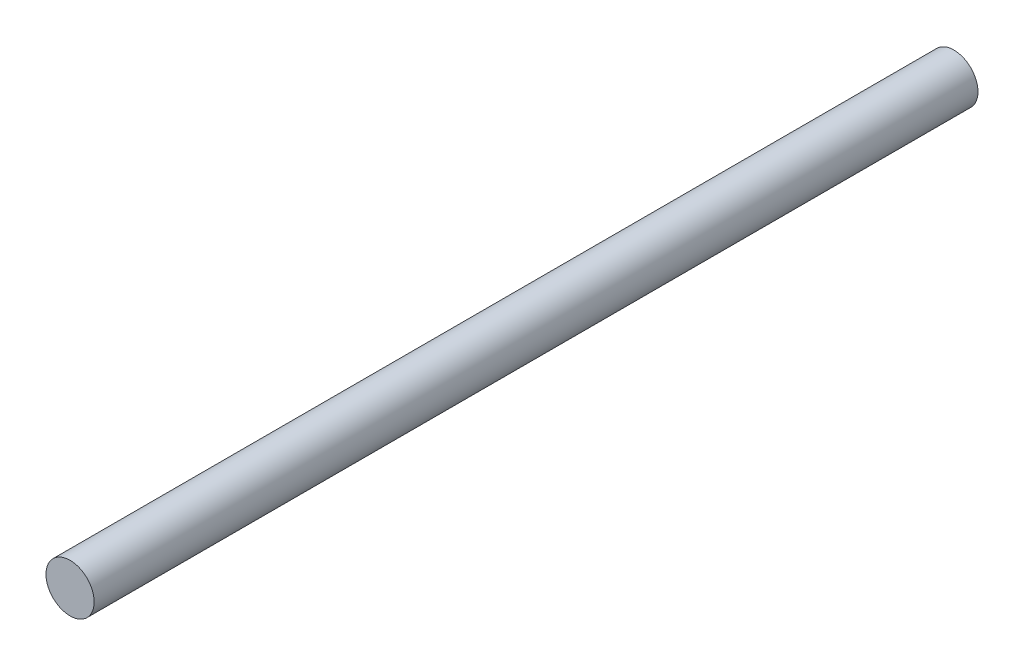
SolidWorks part; units mm, degrees
ref_plane "Front Plane" through (0, 0, 0) normal (0, 0, 1) x (1, 0, 0)
ref_plane "Top Plane" through (0, 0, 0) normal (0, 1, 0) x (1, 0, 0)
ref_plane "Right Plane" through (0, 0, 0) normal (1, 0, 0) x (0, 0, -1)
sketch "Sketch1" plane through (0, 0, 0) normal (0, 0, 1) x (1, 0, 0)
  circle A0 centre (-55.4041, 33.6504) radius 3
extrude "Boss-Extrude1" add sketch "Sketch1" along normal blind 110
